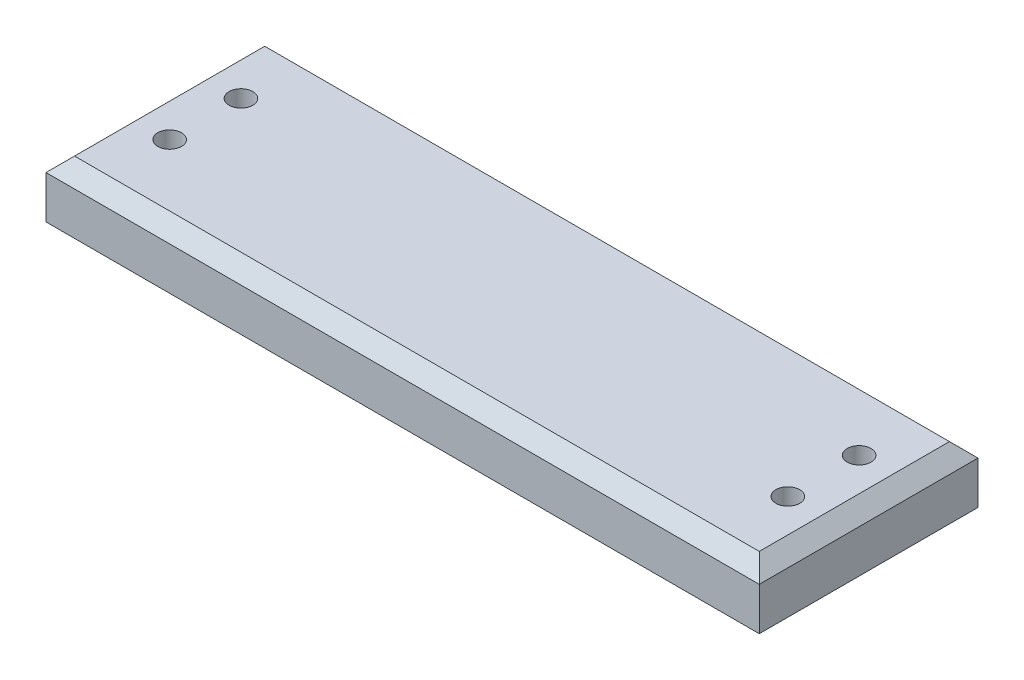
SolidWorks part; units mm, degrees
ref_plane "Front Plane" through (0, 0, 0) normal (0, 0, 1) x (1, 0, 0)
ref_plane "Top Plane" through (0, 0, 0) normal (0, 1, 0) x (1, 0, 0)
ref_plane "Right Plane" through (0, 0, 0) normal (1, 0, 0) x (0, 0, -1)
sketch "Sketch1" plane through (0, 0, 0) normal (0, 1, 0) x (1, 0, 0)
  line L1 (-1905, -584.2) -> (1905, -584.2)
  line L2 (-1905, -584.2) -> (-1905, 584.2)
  line L3 (-1905, 584.2) -> (1905, 584.2)
  line L4 (1905, -584.2) -> (1905, 584.2)
  line L5 (-1905, -584.2) -> (1905, 584.2) construction
  line L6 (-1905, 584.2) -> (1905, -584.2) construction
  point P0 (0, 0)
  dimension "D1" = 3810
  dimension "D2" = 1168.4
extrude "Boss-Extrude1" add sketch "Sketch1" along normal blind 304.8
chamfer "Chamfer1" distance 76.2 angle 45 4 edges at (0, 304.8, 584.2) (-1905, 304.8, 0) (0, 304.8, -584.2) (1905, 304.8, 0)
sketch "Sketch3" plane through (0, 304.8, 0) normal (0, 1, 0) x (1, 0, 0)
  line L0 (-1651, 203.2) -> (1651, 203.2) construction
  line L1 (1651, 203.2) -> (1651, -177.8) construction
  line L2 (1651, -177.8) -> (-1651, -177.8) construction
  line L3 (-1651, -177.8) -> (-1651, 203.2) construction
  line L4 (-1905, -584.2) -> (-1905, 584.2) construction
  line L5 (1905, -584.2) -> (-1905, -584.2) construction
  circle A0 centre (-1651, -177.8) radius 63.5
  circle A1 centre (-1651, 203.2) radius 63.5
  circle A2 centre (1651, 203.2) radius 63.5
  circle A3 centre (1651, -177.8) radius 63.5
  dimension "D5" = 127
  dimension "D6" = 127
  dimension "D7" = 127
  dimension "D8" = 127
  dimension "D1" = 254
  dimension "D2" = 3556
  dimension "D3" = 406.4
  dimension "D4" = 787.4
extrude "Cut-Extrude1" cut sketch "Sketch3" against normal through all
chamfer "Chamfer2" distance 38.1 angle 45 4 edges at (-1651, 0, -139.7) (1651, 0, -139.7) (1651, 0, 241.3) (-1651, 0, 241.3)
